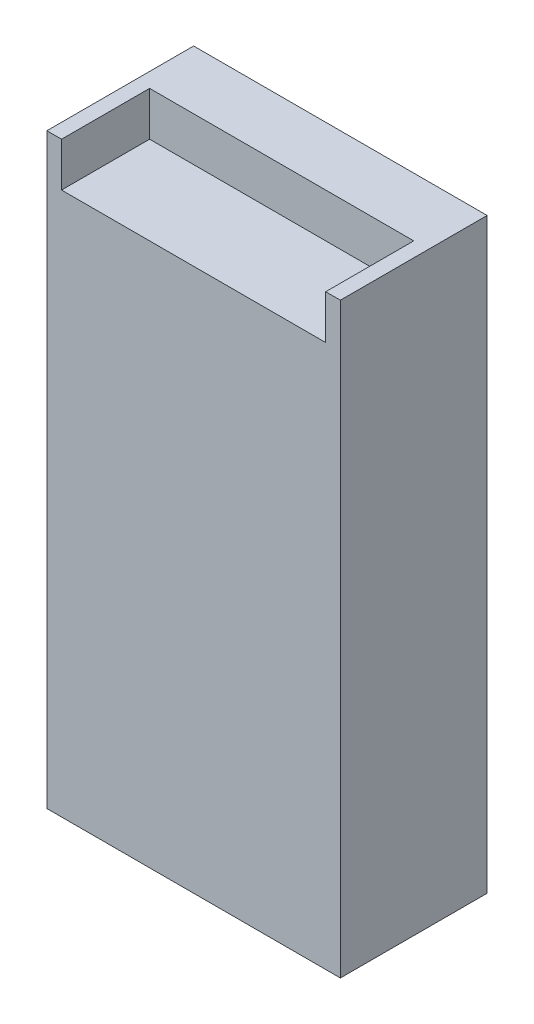
SolidWorks part; units mm, degrees
ref_plane "Front Plane" through (0, 0, 0) normal (0, 0, 1) x (1, 0, 0)
ref_plane "Top Plane" through (0, 0, 0) normal (0, 1, 0) x (1, 0, 0)
ref_plane "Right Plane" through (0, 0, 0) normal (1, 0, 0) x (0, 0, -1)
sketch "Sketch1" plane through (0, 0, 0) normal (0, 0, 1) x (1, 0, 0)
  line L1 (0, 0) -> (100, 0)
  line L2 (0, 0) -> (0, 200)
  line L3 (0, 200) -> (100, 200)
  line L4 (100, 0) -> (100, 200)
  dimension "D1" = 200
  dimension "D2" = 100
extrude "Boss-Extrude1" add sketch "Sketch1" along normal blind 50
sketch "Sketch2" plane through (0, 0, 50) normal (0, 0, 1) x (1, 0, 0)
  line L0 (100, 200) -> (0, 200) construction
  line L1 (5, 200) -> (95, 200)
  line L2 (5, 200) -> (5, 185)
  line L3 (5, 185) -> (95, 185)
  line L4 (95, 200) -> (95, 185)
  line L5 (0, 200) -> (0, 0) construction
  line L6 (100, 0) -> (100, 200) construction
  dimension "D1" = 15
  dimension "D2" = 5
  dimension "D3" = 5
extrude "Cut-Extrude1" cut sketch "Sketch2" against normal blind 30
